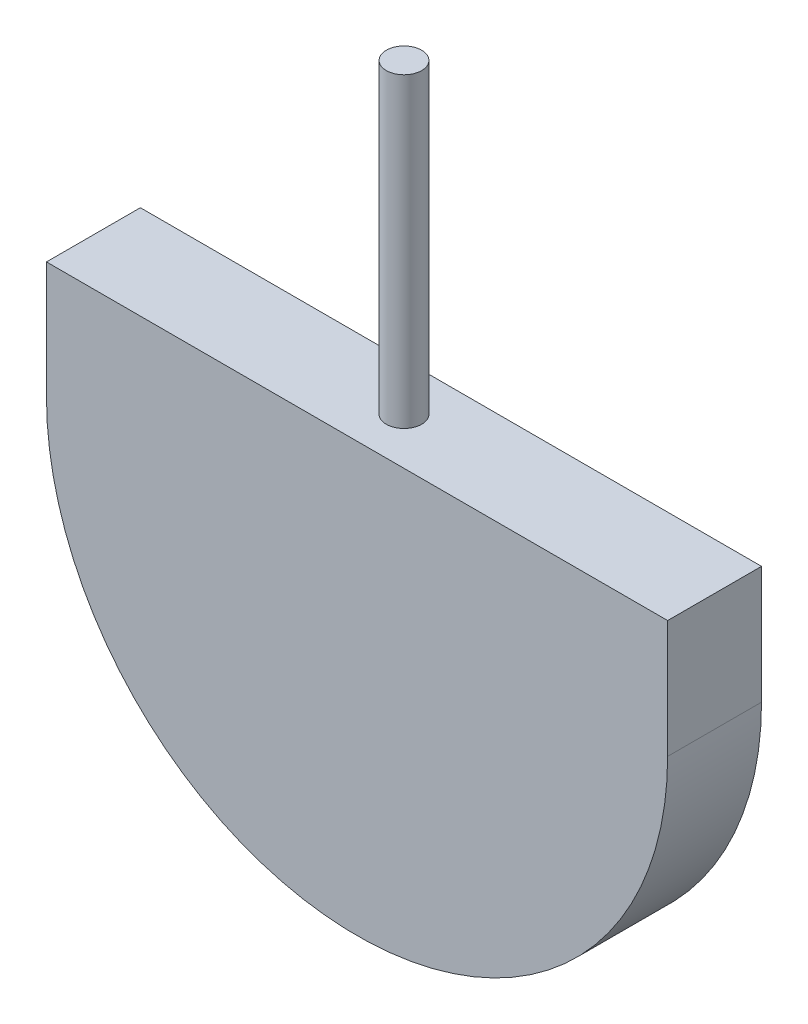
SolidWorks part; units mm, degrees
material "ABS"
ref_plane "Front Plane" through (0, 0, 0) normal (0, 0, 1) x (1, 0, 0)
ref_plane "Top Plane" through (0, 0, 0) normal (0, 1, 0) x (1, 0, 0)
ref_plane "Right Plane" through (0, 0, 0) normal (1, 0, 0) x (0, 0, -1)
sketch "Sketch1" plane through (0, 0, 0) normal (0, 0, 1) x (1, 0, 0)
  line L2 (-13.2, -2.5) -> (-13.2, 2.5)
  line L3 (-13.2, 2.5) -> (13.2, 2.5)
  line L4 (13.2, -2.5) -> (13.2, 2.5)
  line L5 (-13.2, -2.5) -> (13.2, 2.5) construction
  line L6 (-13.2, 2.5) -> (13.2, -2.5) construction
  arc A0 (-13.2, -2.5) -> (13.2, -2.5) centre (0, -2.5) ccw
  point P0 (0, 0)
  dimension "D2" = 13.2
  dimension "D1" = 5
extrude "Boss-Extrude1" add sketch "Sketch1" along normal blind 3.99
sketch "Sketch2" plane through (0, 2.5, 0) normal (0, 1, 0) x (1, 0, 0)
  circle A0 centre (0, -1.995) radius 0.75
  dimension "D1" = 1.5
extrude "Boss-Extrude2" add sketch "Sketch2" along normal up to surface (13.02 mm away)
